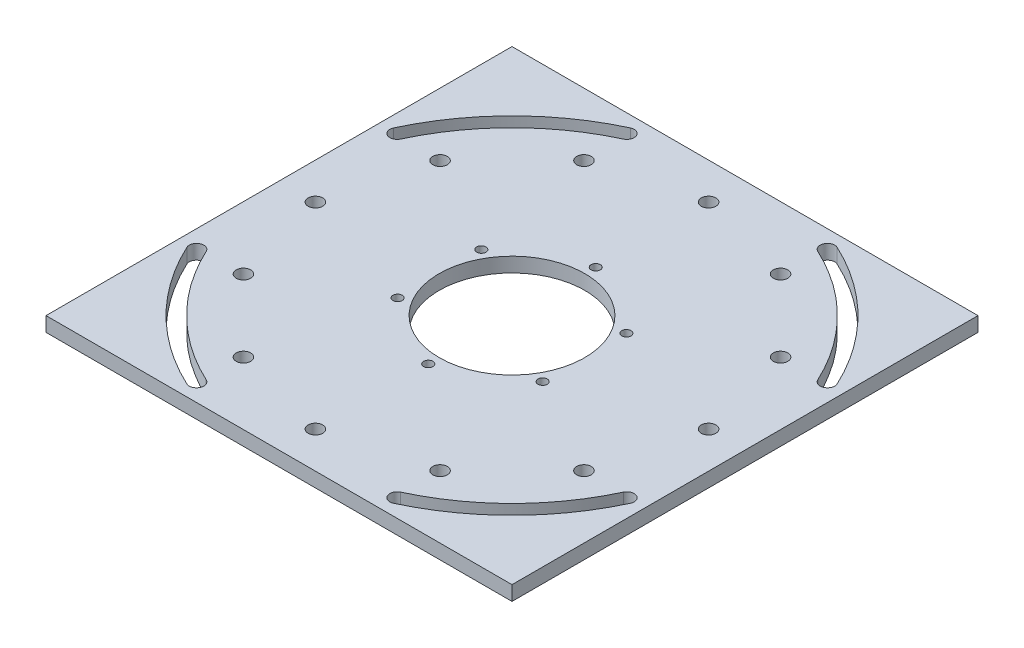
SolidWorks part; units mm, degrees
ref_plane "Front Plane" through (0, 0, 0) normal (0, 0, 1) x (1, 0, 0)
ref_plane "Top Plane" through (0, 0, 0) normal (0, 1, 0) x (1, 0, 0)
ref_plane "Right Plane" through (0, 0, 0) normal (1, 0, 0) x (0, 0, -1)
sketch "Sketch1" plane through (0, 0, 0) normal (0, 1, 0) x (1, 0, 0)
  line L1 (-101.6, 101.6) -> (101.6, 101.6)
  line L2 (-101.6, 101.6) -> (-101.6, -101.6)
  line L3 (-101.6, -101.6) -> (101.6, -101.6)
  line L4 (101.6, 101.6) -> (101.6, -101.6)
  line L5 (-101.6, 101.6) -> (101.6, -101.6) construction
  line L6 (-101.6, -101.6) -> (101.6, 101.6) construction
  point P0 (0, 0)
  dimension "D1" = 203.2
  dimension "D2" = 203.2
extrude "Boss-Extrude1" add sketch "Sketch1" along normal blind 6.35
sketch "Sketch2" plane through (0, 6.35, 0) normal (0, 1, 0) x (1, 0, 0)
  circle A0 centre (0, 0) radius 31.75
  dimension "D1" = 63.5
extrude "Cut-Extrude1" cut sketch "Sketch2" against normal up to next
hole_wizard "1/4 (0.25) Diameter Hole1" positions "Sketch4" profile "Sketch3" hole size "1/4" standard "ANSI Inch" end condition up to next
sketch "Sketch4" plane through (0, 6.35, 0) normal (0, 1, 0) x (1, 0, 0)
  line L0 (0, 0) -> (0, 85.725)
  circle A0 centre (0, 0) radius 85.725
  point P7 (0, 85.725)
  dimension "D1" = 171.45
sketch "Sketch3" plane through (0, 6.35, -85.725) normal (1, 0, 0) x (0, 0, 1)
  line L0 (0, 0) -> (0, 6.351)
  line L1 (0, 6.351) -> (3.175, 6.351)
  line L2 (3.175, 6.351) -> (3.175, 0)
  line L5 (3.175, 0) -> (0, 0)
  line L11 (0, -6.35) -> (0, 107.95) construction
  dimension "Thru Hole Dia." = 6.35
  dimension "Thru Hole Depth" = 6.351
pattern_circular "CirPattern1" count 12 every 30 about axis through (0, 0, 0) along (0, 1, 0) of "1/4 (0.25) Diameter Hole1"
hole_wizard "#10-32 Tapped Hole1" positions "Sketch6" profile "Sketch5" tap size "#10-32" standard "ANSI Inch" end condition up to next
sketch "Sketch6" plane through (0, 6.35, 0) normal (0, 1, 0) x (1, 0, 0)
  line L0 (0, 36.5125) -> (0, 0) construction
  point P0 (0, 36.5125)
  dimension "D1" = 36.5125
sketch "Sketch5" plane through (0, 6.35, -36.5125) normal (1, 0, 0) x (0, 0, 1)
  line L0 (0, 0) -> (0, 6.351)
  line L1 (0, 6.351) -> (2.0193, 6.351)
  line L2 (2.0193, 6.351) -> (2.0193, 0)
  line L5 (2.0193, 0) -> (0, 0)
  line L11 (0, -6.35) -> (0, 107.95) construction
  dimension "Thread Major Dia." = 4.0386
  dimension "Thru Tap Drill Depth" = 6.351
pattern_circular "CirPattern2" count 6 every 60 about axis through (0, 0, 0) along (0, 1, 0) of "#10-32 Tapped Hole1"
sketch "Sketch7" plane through (0, 6.35, 0) normal (0, 1, 0) x (1, 0, 0)
  line L0 (-73.1891, 73.1891) -> (73.1891, -73.1891) construction
  line L1 (73.1891, 73.1891) -> (-73.1891, -73.1891) construction
  line L2 (0, 0) -> (0, 85.725) construction
  line L3 (43.7431, 93.8074) -> (0, 0) construction
  line L4 (93.8074, 43.7431) -> (0, 0) construction
  arc A5 (43.7431, 93.8074) -> (93.8074, 43.7431) centre (0, 0) cw construction
  arc A6 (96.6849, 45.0849) -> (45.0849, 96.6849) centre (0, 0) ccw
  arc A7 (90.9299, 42.4013) -> (42.4013, 90.9299) centre (0, 0) ccw
  arc A8 (90.9299, 42.4013) -> (96.6849, 45.0849) centre (93.8074, 43.7431) ccw
  arc A9 (45.0849, 96.6849) -> (42.4013, 90.9299) centre (43.7431, 93.8074) ccw
  arc A10 (43.7431, -93.8074) -> (93.8074, -43.7431) centre (0, 0) ccw construction
  arc A11 (45.0849, -96.6849) -> (96.6849, -45.0849) centre (0, 0) ccw
  arc A12 (42.4013, -90.9299) -> (90.9299, -42.4013) centre (0, 0) ccw
  arc A13 (42.4013, -90.9299) -> (45.0849, -96.6849) centre (43.7431, -93.8074) ccw
  arc A14 (96.6849, -45.0849) -> (90.9299, -42.4013) centre (93.8074, -43.7431) ccw
  arc A15 (-93.8074, -43.7431) -> (-43.7431, -93.8074) centre (0, 0) ccw construction
  arc A16 (-96.6849, -45.0849) -> (-45.0849, -96.6849) centre (0, 0) ccw
  arc A17 (-90.9299, -42.4013) -> (-42.4013, -90.9299) centre (0, 0) ccw
  arc A18 (-90.9299, -42.4013) -> (-96.6849, -45.0849) centre (-93.8074, -43.7431) ccw
  arc A19 (-45.0849, -96.6849) -> (-42.4013, -90.9299) centre (-43.7431, -93.8074) ccw
  arc A20 (-43.7431, 93.8074) -> (-93.8074, 43.7431) centre (0, 0) ccw construction
  arc A21 (-45.0849, 96.6849) -> (-96.6849, 45.0849) centre (0, 0) ccw
  arc A22 (-42.4013, 90.9299) -> (-90.9299, 42.4013) centre (0, 0) ccw
  arc A23 (-42.4013, 90.9299) -> (-45.0849, 96.6849) centre (-43.7431, 93.8074) ccw
  arc A24 (-96.6849, 45.0849) -> (-90.9299, 42.4013) centre (-93.8074, 43.7431) ccw
  point P9 (73.1891, 73.1891)
  point P17 (73.1891, -73.1891)
  point P25 (-73.1891, -73.1891)
  point P33 (-73.1891, 73.1891)
  dimension "D1" = 3.175
  dimension "D4" = 103.505
  dimension "D2" = 45
  dimension "D3" = 40
extrude "Cut-Extrude2" cut sketch "Sketch7" against normal up to next
